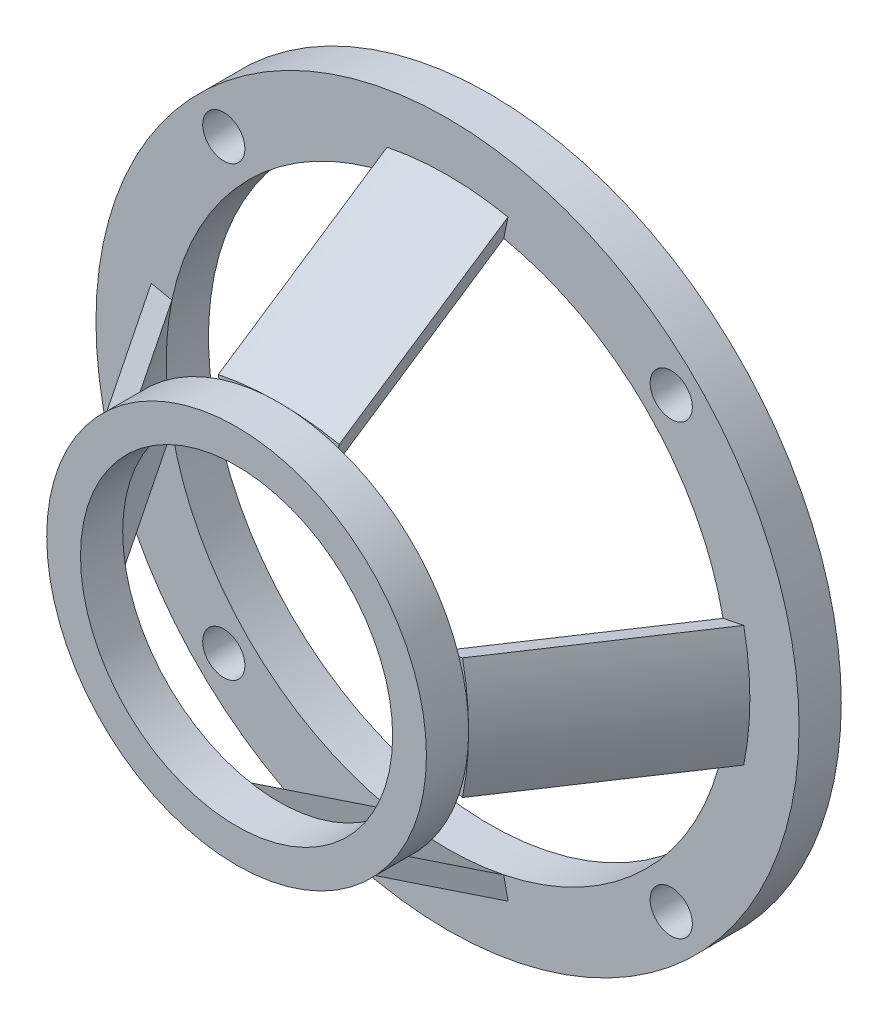
SolidWorks part; units mm, degrees
ref_plane "Front Plane" through (0, 0, 0) normal (0, 0, 1) x (1, 0, 0)
ref_plane "Top Plane" through (0, 0, 0) normal (0, 1, 0) x (1, 0, 0)
ref_plane "Right Plane" through (0, 0, 0) normal (1, 0, 0) x (0, 0, -1)
sketch "Sketch1" plane through (0, 0, 0) normal (0, 0, 1) x (1, 0, 0)
  circle A0 centre (0, 0) radius 25
  circle A1 centre (0, 0) radius 20
  dimension "D1" = 50
  dimension "D2" = 40
extrude "Boss-Extrude1" add sketch "Sketch1" along normal blind 3
ref_plane "Plane1" through (0, 0, 15) normal (0, 0, 1) x (1, 0, 0)
sketch "Sketch7" plane through (0, 0, 15) normal (0, 0, 1) x (1, 0, 0)
  circle A0 centre (0, 0) radius 13.5
  circle A1 centre (0, 0) radius 11.1
  dimension "D1" = 27
  dimension "D2" = 22.2
extrude "Boss-Extrude2" add sketch "Sketch7" along normal blind 3 separate body
sketch "Sketch8" plane through (0, 0, 3) normal (0, 0, 1) x (1, 0, 0)
  line L0 (0, 0) -> (0, 21.5) construction
  line L1 (-4.3, 21.0656) -> (-4, 19.5959)
  line L2 (4, 19.5959) -> (4.3, 21.0656)
  arc A0 (4, 19.5959) -> (-4, 19.5959) centre (0, 0) ccw
  arc A1 (4.3, 21.0656) -> (-4.3, 21.0656) centre (0, 0) ccw
  circle A2 centre (0, 0) radius 21.5 construction
  circle A3 centre (0, 0) radius 20
  circle A4 centre (0, 0) radius 20 construction
  point P12 (0, 20)
  dimension "D3" = 4
  dimension "D4" = 4
  dimension "D1" = 0
  dimension "D2" = 1.5
sketch "Sketch9" plane through (0, 0, 15) normal (0, 0, -1) x (-1, 0, 0)
  line L0 (0, 0) -> (0, 13.5) construction
  line L1 (0, 0) -> (0, 21.5) construction
  circle A0 centre (0, 0) radius 13.5 construction
  point P8 (0, 13.5)
sketch3d "3DSketch3"
  line L0 (0, 21.5, 3) -> (0, 13.5, 15)
sweep "Sweep1" add profiles "Sketch8" path "3DSketch3"
sketch "Sketch4" plane through (0, 0, 0) normal (0, 1, 0) x (1, 0, 0)
  line L0 (0, 0) -> (0, -11.6407) construction
pattern_circular "CirPattern2" count 4 over 360 about axis through (0, 0, 0) along (0, 0, 1) of "Sweep1"
sketch "Sketch3" plane through (0, 0, 3) normal (0, 0, 1) x (1, 0, 0)
  line L0 (0, 0) -> (0, 22.5) construction
  line L1 (0, 0) -> (15.9099, 15.9099) construction
  circle A2 centre (15.9099, 15.9099) radius 1.5
  dimension "D1" = 22.5
  dimension "D4" = 3
  dimension "D2" = 22.5
  dimension "D3" = 45
extrude "Cut-Extrude1" cut sketch "Sketch3" against normal through all
pattern_circular "CirPattern1" count 4 over 360 about axis through (0, 0, 0) along (0, 0, 1) of "Cut-Extrude1"
equation "\"D4@Sketch8\"=\"D3@Sketch8\""
